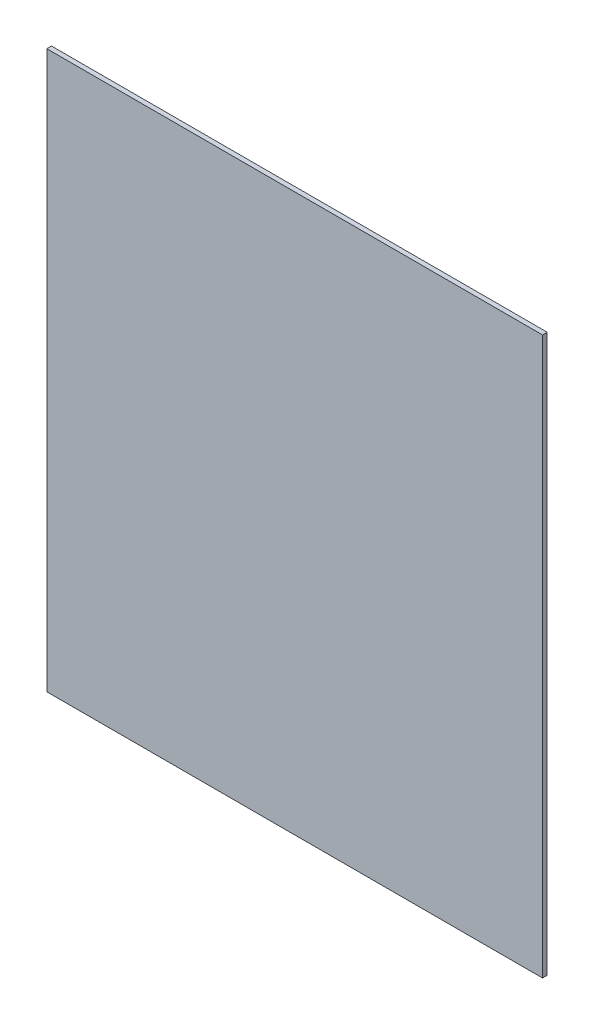
SolidWorks part; units mm, degrees
ref_plane "Front Plane" through (0, 0, 0) normal (0, 0, 1) x (1, 0, 0)
ref_plane "Top Plane" through (0, 0, 0) normal (0, 1, 0) x (1, 0, 0)
ref_plane "Right Plane" through (0, 0, 0) normal (1, 0, 0) x (0, 0, -1)
sketch "Sketch1" plane through (0, 0, 0) normal (0, 0, 1) x (1, 0, 0)
  line L1 (-64.2938, -72.2313) -> (64.2938, -72.2313)
  line L2 (-64.2938, -72.2313) -> (-64.2938, 72.2313)
  line L3 (-64.2938, 72.2313) -> (64.2938, 72.2313)
  line L4 (64.2938, -72.2313) -> (64.2938, 72.2313)
  line L5 (-64.2938, -72.2313) -> (64.2938, 72.2313) construction
  line L6 (-64.2938, 72.2313) -> (64.2938, -72.2313) construction
  point P0 (0, 0)
  dimension "D1" = 128.5875
  dimension "D2" = 144.4625
extrude "Boss-Extrude1" add sketch "Sketch1" along normal blind 1.2141 contours L3 L4 L1 L2
